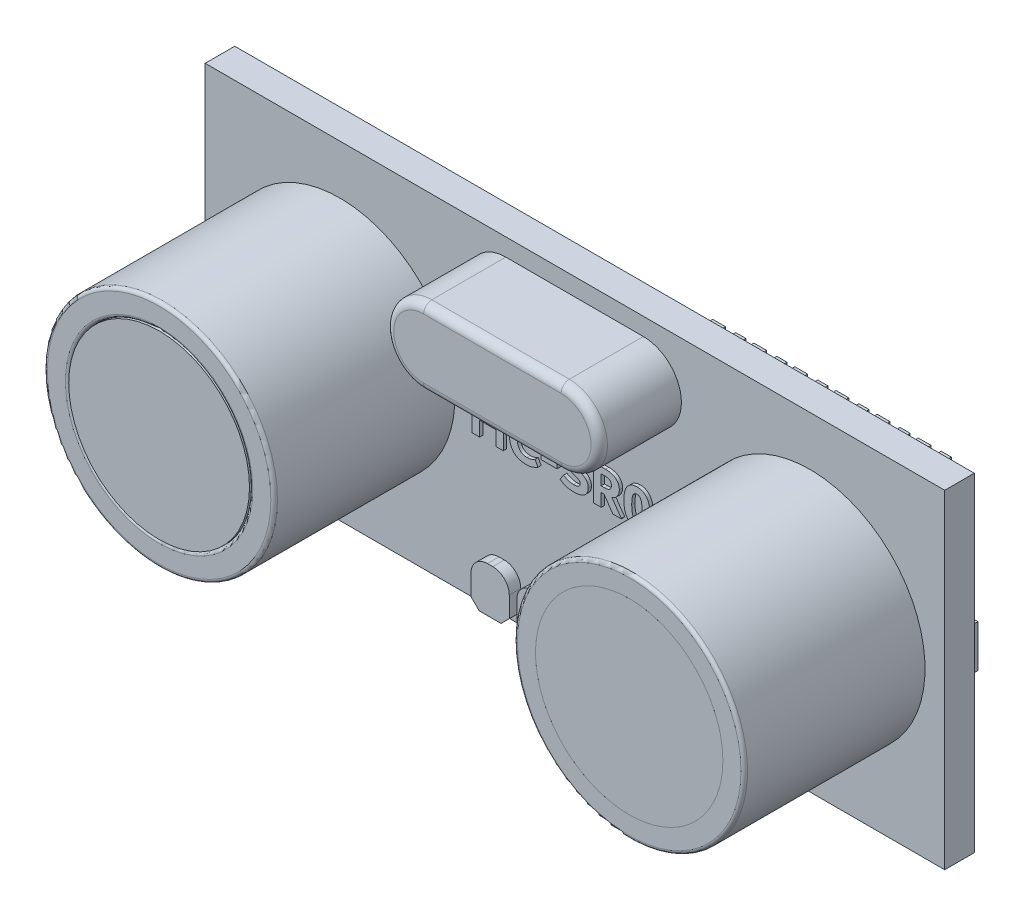
SolidWorks part; units mm, degrees
ref_plane "Front Plane" through (0, 0, 0) normal (0, 0, 1) x (1, 0, 0)
ref_plane "Top Plane" through (0, 0, 0) normal (0, 1, 0) x (1, 0, 0)
ref_plane "Right Plane" through (0, 0, 0) normal (1, 0, 0) x (0, 0, -1)
sketch "Sketch2" plane through (0, 0, 0) normal (0, 0, 1) x (1, 0, 0)
  line L1 (22.5, 10) -> (-22.5, 10)
  line L2 (22.5, 10) -> (22.5, -10)
  line L3 (22.5, -10) -> (-22.5, -10)
  line L4 (-22.5, 10) -> (-22.5, -10)
  line L5 (22.5, 10) -> (-22.5, -10) construction
  line L6 (22.5, -10) -> (-22.5, 10) construction
  point P0 (0, 0)
  dimension "D1" = 45
  dimension "D2" = 20
extrude "Boss-Extrude1" add sketch "Sketch2" along normal blind 1.8
sketch "Sketch3" plane through (0, 0, 1.8) normal (0, 0, 1) x (1, 0, 0)
  line L0 (0, 0) -> (0, -10) construction
  line L1 (-22.5, -10) -> (22.5, -10) construction
  line L2 (-22.5, 10) -> (-22.5, -10) construction
  line L3 (-22.5, 0) -> (22.5, 0) construction
  line L4 (22.5, -10) -> (22.5, 10) construction
  circle A0 centre (-14.3027, 0) radius 7
  circle A1 centre (-14.3027, 0) radius 5.5
  circle A2 centre (14.3027, 0) radius 5.5
  circle A3 centre (14.3027, 0) radius 7
extrude "Boss-Extrude2" add sketch "Sketch3" along normal blind 11
sketch "Sketch4" plane through (0, 0, 1.8) normal (0, 0, 1) x (1, 0, 0)
  line L0 (0, 0) -> (0, 5.0118) construction
  circle A0 centre (-14.3814, -0.1625) radius 3.6066
  circle A1 centre (14.3814, -0.1625) radius 3.6066
extrude "Boss-Extrude3" add sketch "Sketch4" along normal blind 3
sketch "Sketch5" plane through (0, 0, 1.8) normal (0, 0, 1) x (1, 0, 0)
  line L0 (0, 0) -> (0, 10) construction
  line L1 (22.5, 10) -> (-22.5, 10) construction
  line L2 (-4.2079, 6.6167) -> (4.1609, 6.6167) construction
  line L3 (-4.2079, 8.9335) -> (4.1609, 8.9335)
  line L4 (-4.2079, 4.2999) -> (4.1609, 4.2999)
  arc A0 (-4.2079, 8.9335) -> (-4.2079, 4.2999) centre (-4.2079, 6.6167) ccw
  arc A1 (4.1609, 4.2999) -> (4.1609, 8.9335) centre (4.1609, 6.6167) ccw
  point P7 (-0.0235, 6.6167)
extrude "Boss-Extrude4" add sketch "Sketch5" along normal blind 5
fillet "Fillet1" radius 0.5 4 edges at (-0.0235, 8.9335, 6.8) (6.4777, 6.6167, 6.8) (-0.0235, 4.2999, 6.8) (-6.5247, 6.6167, 6.8)
fillet "Fillet2" radius 0.2 4 edges at (8.8027, 0, 12.8) (7.3027, 0, 12.8) (-8.8027, 0, 12.8) (-7.3027, 0, 12.8)
sketch "Sketch6" plane through (0, 0, 12.8) normal (0, 0, 1) x (1, 0, 0)
  circle A0 centre (-14.3027, 0) radius 5.5
extrude "Boss-Extrude5" add sketch "Sketch6" against normal blind 0.2 separate body
sketch "Sketch7" plane through (0, 0, 12.8) normal (0, 0, 1) x (1, 0, 0)
  line L0 (0, 0) -> (0, -10.0616) construction
sketch "Sketch8" plane through (0, 0, 12.8) normal (0, 0, 1) x (1, 0, 0)
  circle A0 centre (14.3027, 0) radius 5.7
  circle A1 centre (14.3027, 0) radius 5.7
  circle M1 centre (14.3027, 0) radius 5.7
extrude "Boss-Extrude7" add sketch "Sketch8" against normal blind 0.3 separate body contours M1
sketch "Sketch9" plane through (0, 0, 1.8) normal (0, 0, 1) x (1, 0, 0)
  line L1 (-4.6238, -7.073) -> (-4.2964, -7.073)
  line L2 (-5.6238, -8.073) -> (-5.6238, -9.3177)
  line L3 (-5.1238, -9.8177) -> (-3.7964, -9.8177)
  line L4 (5.517, -8.073) -> (5.517, -9.3177)
  line L5 (2.9757, -9.3177) -> (3.4757, -9.8177)
  line L6 (5.517, -9.3177) -> (5.017, -9.8177)
  line L7 (-3.2964, -8.073) -> (-3.2964, -9.3177)
  line L8 (-2.8358, -8.073) -> (-2.8358, -9.3177)
  line L9 (-0.2685, -8.073) -> (-0.2685, -9.3177)
  line L10 (0.2992, -8.073) -> (0.2992, -9.3177)
  line L11 (3.9757, -7.073) -> (4.517, -7.073)
  line L12 (2.5161, -8.073) -> (2.5161, -9.3177)
  line L13 (2.9757, -8.073) -> (2.9757, -9.3177)
  line L14 (0.7992, -9.8177) -> (2.0161, -9.8177)
  line L15 (5.517, -11.7299) -> (5.7333, -11.7299)
  line L16 (1.2992, -7.073) -> (1.5161, -7.073)
  line L17 (-1.8358, -7.073) -> (-1.2685, -7.073)
  line L18 (-2.3358, -9.8177) -> (-0.7685, -9.8177)
  line L19 (3.4757, -9.8177) -> (5.017, -9.8177)
  line L20 (-5.6238, -9.3177) -> (-5.1238, -9.8177)
  line L21 (-3.7964, -9.8177) -> (-3.2964, -9.3177)
  line L22 (-2.8358, -9.3177) -> (-2.3358, -9.8177)
  line L23 (-0.2685, -9.3177) -> (-0.7685, -9.8177)
  line L24 (0.2992, -9.3177) -> (0.7992, -9.8177)
  line L25 (2.5161, -9.3177) -> (2.0161, -9.8177)
  line L26 (-0.2685, -8.48) -> (-0.2325, -8.4894) construction
  line L28 (-0.2685, -8.4983) -> (-0.2325, -8.4894) construction
  arc A0 (-4.6238, -7.073) -> (-5.6238, -8.073) centre (-4.6238, -8.073) ccw
  arc A1 (5.517, -8.073) -> (4.517, -7.073) centre (4.517, -8.073) ccw
  arc A2 (2.9757, -8.073) -> (3.9757, -7.073) centre (3.9757, -8.073) cw
  arc A3 (2.5161, -8.073) -> (1.5161, -7.073) centre (1.5161, -8.073) ccw
  arc A4 (0.2992, -8.073) -> (1.2992, -7.073) centre (1.2992, -8.073) cw
  arc A5 (-0.2685, -8.073) -> (-1.2685, -7.073) centre (-1.2685, -8.073) ccw
  arc A6 (-2.8358, -8.073) -> (-1.8358, -7.073) centre (-1.8358, -8.073) cw
  arc A7 (-3.2964, -8.073) -> (-4.2964, -7.073) centre (-4.2964, -8.073) ccw
  point P0 (-0.2325, -8.4894)
  point P8 (-3.2964, -9.8177)
  point P10 (-2.8358, -9.8177)
  point P12 (-0.2685, -9.8177)
  point P14 (0.2992, -9.8177)
  point P17 (2.5161, -9.8177)
  point P19 (2.9757, -9.8177)
  point P22 (5.517, -9.8177)
  point P30 (2.9757, -7.073)
  point P35 (0.2992, -7.073)
  point P40 (-2.8358, -7.073)
  dimension "D1" = 1
  dimension "D2" = 1
extrude "Boss-Extrude8" add sketch "Sketch9" along normal blind 0.7 contours L7 A7 L1 A0 L2 L20 L3 L21 | A6 L8 L22 L18 L23 L9 A5 L17 | A2 L13 L5 L19 L6 L4 A1 L11 | A4 L10 L24 L14 L25 L12 A3 L16
sketch "Sketch12" plane through (0, 0, 0) normal (0, 0, -1) x (-1, 0, 0)
  line L1 (-21.7259, 1.2905) -> (-14.7282, 1.2905)
  line L2 (-21.7259, 1.2905) -> (-21.7259, -1.2905)
  line L3 (-21.7259, -1.2905) -> (-14.7282, -1.2905)
  line L4 (-14.7282, 1.2905) -> (-14.7282, -1.2905)
  line L5 (-21.7259, 1.2905) -> (-14.7282, -1.2905) construction
  line L6 (-21.7259, -1.2905) -> (-14.7282, 1.2905) construction
  line L7 (-8.1561, 1.2905) -> (-0.8747, 1.2905)
  line L8 (-8.1561, 1.2905) -> (-8.1561, -1.2905)
  line L9 (-8.1561, -1.2905) -> (-0.8747, -1.2905)
  line L10 (-0.8747, 1.2905) -> (-0.8747, -1.2905)
  line L11 (-8.1561, 1.2905) -> (-0.8747, -1.2905) construction
  line L12 (-8.1561, -1.2905) -> (-0.8747, 1.2905) construction
  line L13 (12.7897, 4.0523) -> (16.3831, 4.0523)
  line L14 (12.7897, 4.0523) -> (12.7897, -3.1345)
  line L15 (12.7897, -3.1345) -> (16.3831, -3.1345)
  line L16 (16.3831, 4.0523) -> (16.3831, -3.1345)
  line L17 (12.7897, 4.0523) -> (16.3831, -3.1345) construction
  line L18 (12.7897, -3.1345) -> (16.3831, 4.0523) construction
  point P0 (-18.227, 0)
  point P5 (-4.5154, 0)
  point P10 (14.5864, 0.4589)
extrude "Boss-Extrude9" add sketch "Sketch12" along normal blind 1
sketch "Sketch13" plane through (0, 0, 0) normal (0, 0, -1) x (-1, 0, 0)
  line L0 (-17.8032, 9.3509) -> (-17.8032, 7.6448)
  line L1 (-20.3032, 9.3509) -> (-19.6828, 9.3509)
  line L2 (-20.3032, 9.3509) -> (-20.3032, 7.6448)
  line L3 (-20.3032, 7.6448) -> (-19.6828, 7.6448)
  line L4 (-19.6828, 9.3509) -> (-19.6828, 7.6448)
  line L5 (-20.3032, 9.3509) -> (-19.6828, 7.6448) construction
  line L6 (-20.3032, 7.6448) -> (-19.6828, 9.3509) construction
  line L7 (-19.0624, 9.3509) -> (-18.2869, 9.3509)
  line L8 (-19.0624, 9.3509) -> (-19.0624, 7.6448)
  line L9 (-19.0624, 7.6448) -> (-18.2869, 7.6448)
  line L10 (-18.2869, 9.3509) -> (-18.2869, 7.6448)
  line L11 (-19.0624, 9.3509) -> (-18.2869, 7.6448) construction
  line L12 (-19.0624, 7.6448) -> (-18.2869, 9.3509) construction
  line L13 (-17.8032, 9.3509) -> (-17.1828, 9.3509)
  line L14 (-17.1828, 9.3509) -> (-17.1828, 7.6448)
  line L15 (-17.8032, 7.6448) -> (-17.1828, 7.6448)
  line L16 (-17.8032, 7.6448) -> (-17.1828, 9.3509) construction
  line L17 (-17.8032, 9.3509) -> (-17.1828, 7.6448) construction
  line L18 (-16.5624, 9.3509) -> (-16.5624, 7.6448)
  line L19 (-16.5624, 7.6448) -> (-15.7869, 7.6448)
  line L20 (-16.5624, 7.6448) -> (-15.7869, 9.3509) construction
  line L21 (-16.5624, 9.3509) -> (-15.7869, 7.6448) construction
  line L22 (-16.5624, 9.3509) -> (-15.7869, 9.3509)
  line L23 (-15.7869, 9.3509) -> (-15.7869, 7.6448)
  line L24 (-15.3032, 9.3509) -> (-15.3032, 7.6448)
  line L25 (-15.3032, 9.3509) -> (-14.6828, 9.3509)
  line L26 (-14.6828, 9.3509) -> (-14.6828, 7.6448)
  line L27 (-15.3032, 7.6448) -> (-14.6828, 7.6448)
  line L28 (-15.3032, 7.6448) -> (-14.6828, 9.3509) construction
  line L29 (-15.3032, 9.3509) -> (-14.6828, 7.6448) construction
  line L30 (-14.0624, 9.3509) -> (-14.0624, 7.6448)
  line L31 (-14.0624, 7.6448) -> (-13.2869, 7.6448)
  line L32 (-14.0624, 7.6448) -> (-13.2869, 9.3509) construction
  line L33 (-14.0624, 9.3509) -> (-13.2869, 7.6448) construction
  line L34 (-14.0624, 9.3509) -> (-13.2869, 9.3509)
  line L35 (-13.2869, 9.3509) -> (-13.2869, 7.6448)
  line L36 (-12.8032, 9.3509) -> (-12.8032, 7.6448)
  line L37 (-12.8032, 9.3509) -> (-12.1828, 9.3509)
  line L38 (-12.1828, 9.3509) -> (-12.1828, 7.6448)
  line L39 (-12.8032, 7.6448) -> (-12.1828, 7.6448)
  line L40 (-12.8032, 7.6448) -> (-12.1828, 9.3509) construction
  line L41 (-12.8032, 9.3509) -> (-12.1828, 7.6448) construction
  line L42 (-11.5624, 9.3509) -> (-11.5624, 7.6448)
  line L43 (-11.5624, 7.6448) -> (-10.7869, 7.6448)
  line L44 (-11.5624, 7.6448) -> (-10.7869, 9.3509) construction
  line L45 (-11.5624, 9.3509) -> (-10.7869, 7.6448) construction
  line L46 (-11.5624, 9.3509) -> (-10.7869, 9.3509)
  line L47 (-10.7869, 9.3509) -> (-10.7869, 7.6448)
  line L48 (-10.3032, 9.3509) -> (-10.3032, 7.6448)
  line L49 (-10.3032, 9.3509) -> (-9.6828, 9.3509)
  line L50 (-9.6828, 9.3509) -> (-9.6828, 7.6448)
  line L51 (-10.3032, 7.6448) -> (-9.6828, 7.6448)
  line L52 (-10.3032, 7.6448) -> (-9.6828, 9.3509) construction
  line L53 (-10.3032, 9.3509) -> (-9.6828, 7.6448) construction
  line L54 (-9.0624, 9.3509) -> (-9.0624, 7.6448)
  line L55 (-9.0624, 7.6448) -> (-8.2869, 7.6448)
  line L56 (-9.0624, 7.6448) -> (-8.2869, 9.3509) construction
  line L57 (-9.0624, 9.3509) -> (-8.2869, 7.6448) construction
  line L58 (-9.0624, 9.3509) -> (-8.2869, 9.3509)
  line L59 (-8.2869, 9.3509) -> (-8.2869, 7.6448)
  line L60 (-7.8032, 9.3509) -> (-7.8032, 7.6448)
  line L61 (-7.8032, 9.3509) -> (-7.1828, 9.3509)
  line L62 (-7.1828, 9.3509) -> (-7.1828, 7.6448)
  line L63 (-7.8032, 7.6448) -> (-7.1828, 7.6448)
  line L64 (-7.8032, 7.6448) -> (-7.1828, 9.3509) construction
  line L65 (-7.8032, 9.3509) -> (-7.1828, 7.6448) construction
  line L66 (-6.5624, 9.3509) -> (-6.5624, 7.6448)
  line L67 (-6.5624, 7.6448) -> (-5.7869, 7.6448)
  line L68 (-6.5624, 7.6448) -> (-5.7869, 9.3509) construction
  line L69 (-6.5624, 9.3509) -> (-5.7869, 7.6448) construction
  line L70 (-6.5624, 9.3509) -> (-5.7869, 9.3509)
  line L71 (-5.7869, 9.3509) -> (-5.7869, 7.6448)
  line L72 (-17.8032, -4.6491) -> (-17.8032, -6.3552)
  line L73 (-17.8032, -4.6491) -> (-17.1828, -4.6491)
  line L74 (-17.1828, -4.6491) -> (-17.1828, -6.3552)
  line L75 (-17.8032, -6.3552) -> (-17.1828, -6.3552)
  line L76 (-17.8032, -6.3552) -> (-17.1828, -4.6491) construction
  line L77 (-17.8032, -4.6491) -> (-17.1828, -6.3552) construction
  line L78 (-16.5624, -4.6491) -> (-16.5624, -6.3552)
  line L79 (-16.5624, -6.3552) -> (-15.7869, -6.3552)
  line L80 (-16.5624, -6.3552) -> (-15.7869, -4.6491) construction
  line L81 (-16.5624, -4.6491) -> (-15.7869, -6.3552) construction
  line L82 (-16.5624, -4.6491) -> (-15.7869, -4.6491)
  line L83 (-15.7869, -4.6491) -> (-15.7869, -6.3552)
  line L84 (-15.3032, -4.6491) -> (-15.3032, -6.3552)
  line L85 (-15.3032, -4.6491) -> (-14.6828, -4.6491)
  line L86 (-14.6828, -4.6491) -> (-14.6828, -6.3552)
  line L87 (-15.3032, -6.3552) -> (-14.6828, -6.3552)
  line L88 (-15.3032, -6.3552) -> (-14.6828, -4.6491) construction
  line L89 (-15.3032, -4.6491) -> (-14.6828, -6.3552) construction
  line L90 (-14.0624, -4.6491) -> (-14.0624, -6.3552)
  line L91 (-14.0624, -6.3552) -> (-13.2869, -6.3552)
  line L92 (-14.0624, -6.3552) -> (-13.2869, -4.6491) construction
  line L93 (-14.0624, -4.6491) -> (-13.2869, -6.3552) construction
  line L94 (-14.0624, -4.6491) -> (-13.2869, -4.6491)
  line L95 (-13.2869, -4.6491) -> (-13.2869, -6.3552)
  line L96 (-12.8032, -4.6491) -> (-12.8032, -6.3552)
  line L97 (-12.8032, -4.6491) -> (-12.1828, -4.6491)
  line L98 (-12.1828, -4.6491) -> (-12.1828, -6.3552)
  line L99 (-12.8032, -6.3552) -> (-12.1828, -6.3552)
  line L100 (-12.8032, -6.3552) -> (-12.1828, -4.6491) construction
  line L101 (-12.8032, -4.6491) -> (-12.1828, -6.3552) construction
  line L102 (-11.5624, -4.6491) -> (-11.5624, -6.3552)
  line L103 (-11.5624, -6.3552) -> (-10.7869, -6.3552)
  line L104 (-11.5624, -6.3552) -> (-10.7869, -4.6491) construction
  line L105 (-11.5624, -4.6491) -> (-10.7869, -6.3552) construction
  line L106 (-11.5624, -4.6491) -> (-10.7869, -4.6491)
  line L107 (-10.7869, -4.6491) -> (-10.7869, -6.3552)
  line L108 (-10.3032, -4.6491) -> (-10.3032, -6.3552)
  line L109 (-10.3032, -4.6491) -> (-9.6828, -4.6491)
  line L110 (-9.6828, -4.6491) -> (-9.6828, -6.3552)
  line L111 (-10.3032, -6.3552) -> (-9.6828, -6.3552)
  line L112 (-10.3032, -6.3552) -> (-9.6828, -4.6491) construction
  line L113 (-10.3032, -4.6491) -> (-9.6828, -6.3552) construction
  line L114 (-9.0624, -4.6491) -> (-9.0624, -6.3552)
  line L115 (-9.0624, -6.3552) -> (-8.2869, -6.3552)
  line L116 (-9.0624, -6.3552) -> (-8.2869, -4.6491) construction
  line L117 (-9.0624, -4.6491) -> (-8.2869, -6.3552) construction
  line L118 (-9.0624, -4.6491) -> (-8.2869, -4.6491)
  line L119 (-8.2869, -4.6491) -> (-8.2869, -6.3552)
  line L120 (-7.8032, -4.6491) -> (-7.8032, -6.3552)
  line L121 (-7.8032, -4.6491) -> (-7.1828, -4.6491)
  line L122 (-7.1828, -4.6491) -> (-7.1828, -6.3552)
  line L123 (-7.8032, -6.3552) -> (-7.1828, -6.3552)
  line L124 (-7.8032, -6.3552) -> (-7.1828, -4.6491) construction
  line L125 (-7.8032, -4.6491) -> (-7.1828, -6.3552) construction
  line L126 (-6.5624, -4.6491) -> (-6.5624, -6.3552)
  line L127 (-6.5624, -6.3552) -> (-5.7869, -6.3552)
  line L128 (-6.5624, -6.3552) -> (-5.7869, -4.6491) construction
  line L129 (-6.5624, -4.6491) -> (-5.7869, -6.3552) construction
  line L130 (-6.5624, -4.6491) -> (-5.7869, -4.6491)
  line L131 (-5.7869, -4.6491) -> (-5.7869, -6.3552)
  line L132 (-20.3032, -4.6491) -> (-20.3032, -6.3552)
  line L133 (-20.3032, -4.6491) -> (-19.6828, -4.6491)
  line L134 (-19.6828, -4.6491) -> (-19.6828, -6.3552)
  line L135 (-20.3032, -6.3552) -> (-19.6828, -6.3552)
  line L136 (-20.3032, -6.3552) -> (-19.6828, -4.6491) construction
  line L137 (-20.3032, -4.6491) -> (-19.6828, -6.3552) construction
  line L138 (-19.0624, -4.6491) -> (-19.0624, -6.3552)
  line L139 (-19.0624, -6.3552) -> (-18.2869, -6.3552)
  line L140 (-19.0624, -6.3552) -> (-18.2869, -4.6491) construction
  line L141 (-19.0624, -4.6491) -> (-18.2869, -6.3552) construction
  line L142 (-19.0624, -4.6491) -> (-18.2869, -4.6491)
  line L143 (-18.2869, -4.6491) -> (-18.2869, -6.3552)
  point P0 (-19.993, 8.4978)
  point P5 (-18.6746, 8.4978)
  dimension "D1" = 6
  dimension "D2" = 2
extrude "Boss-Extrude10" add sketch "Sketch13" along normal blind 0.8
sketch "Sketch15" plane through (0, 0, 0) normal (0, 0, -1) x (-1, 0, 0)
  line L0 (4.8255, 2.9186) -> (4.0469, 2.9186)
  line L1 (4.8255, 0.7912) -> (4.8255, -1.0904)
  line L2 (4.8255, 0.7912) -> (4.0469, 0.7912)
  line L3 (4.0469, 0.7912) -> (4.0469, -1.0904)
  line L4 (4.8255, -1.0904) -> (4.0469, -1.0904)
  line L5 (4.8255, 0.7912) -> (4.0469, -1.0904) construction
  line L6 (4.0469, 0.7912) -> (4.8255, -1.0904) construction
  line L7 (4.8255, 4.8002) -> (4.0469, 2.9186) construction
  line L8 (4.0469, 4.8002) -> (4.0469, 2.9186)
  line L9 (4.8255, 4.8002) -> (4.0469, 4.8002)
  line L10 (4.0469, 4.8002) -> (4.8255, 2.9186) construction
  line L11 (4.8255, 4.8002) -> (4.8255, 2.9186)
  line L12 (3.2077, 0.7103) -> (2.4291, 0.7103)
  line L13 (3.2077, 2.592) -> (3.2077, 0.7103)
  line L14 (3.2077, 2.592) -> (2.4291, 0.7103) construction
  line L15 (3.2077, 2.592) -> (2.4291, 2.592)
  line L16 (2.4291, 2.592) -> (2.4291, 0.7103)
  line L17 (2.4291, 2.592) -> (3.2077, 0.7103) construction
  line L18 (14.3374, -7.7932) -> (16.2191, -7.7932)
  line L19 (14.0108, -5.3969) -> (14.0108, -6.1755)
  line L20 (12.1292, -5.3969) -> (12.1292, -6.1755)
  line L21 (18.0198, -5.3969) -> (18.0198, -6.1755)
  line L22 (12.1292, -6.1755) -> (14.0108, -6.1755)
  line L23 (16.1382, -5.3969) -> (16.1382, -6.1755)
  line L24 (14.3374, -7.0146) -> (16.2191, -7.0146)
  line L25 (12.1292, -5.3969) -> (14.0108, -5.3969)
  line L26 (12.1292, -6.1755) -> (14.0108, -5.3969) construction
  line L27 (14.3374, -7.0146) -> (16.2191, -7.7932) construction
  line L28 (12.1292, -5.3969) -> (14.0108, -6.1755) construction
  line L29 (14.3374, -7.0146) -> (14.3374, -7.7932)
  line L30 (16.2191, -7.0146) -> (16.2191, -7.7932)
  line L31 (16.1382, -6.1755) -> (18.0198, -5.3969) construction
  line L32 (16.1382, -6.1755) -> (18.0198, -6.1755)
  line L33 (16.1382, -5.3969) -> (18.0198, -6.1755) construction
  line L34 (16.1382, -5.3969) -> (18.0198, -5.3969)
  line L35 (14.3374, -7.7932) -> (16.2191, -7.0146) construction
  line L36 (-12.3479, 3.2689) -> (-12.3479, 2.4903)
  line L37 (-10.4663, 3.2689) -> (-10.4663, 2.4903)
  line L38 (-12.3479, 3.2689) -> (-10.4663, 2.4903) construction
  line L39 (-12.3479, 2.4903) -> (-10.4663, 2.4903)
  line L40 (-12.3479, 2.4903) -> (-10.4663, 3.2689) construction
  line L41 (-12.3479, 3.2689) -> (-10.4663, 3.2689)
  line L42 (0.5142, 8.9122) -> (0.5142, 8.1336)
  line L43 (12.9207, 8.9122) -> (12.9207, 8.1336)
  line L44 (0.5142, 8.1336) -> (2.3958, 8.9122) construction
  line L45 (18.8113, 8.9122) -> (18.8113, 8.1336)
  line L46 (16.9297, 8.1336) -> (18.8113, 8.9122) construction
  line L47 (16.9297, 8.9122) -> (16.9297, 8.1336)
  line L48 (2.3958, 8.9122) -> (2.3958, 8.1336)
  line L49 (12.9207, 8.1336) -> (14.8024, 8.1336)
  line L50 (12.9207, 8.9122) -> (14.8024, 8.1336) construction
  line L51 (0.5142, 8.1336) -> (2.3958, 8.1336)
  line L52 (0.5142, 8.9122) -> (2.3958, 8.9122)
  line L53 (14.8024, 8.9122) -> (14.8024, 8.1336)
  line L54 (12.9207, 8.9122) -> (14.8024, 8.9122)
  line L55 (16.9297, 8.1336) -> (18.8113, 8.1336)
  line L56 (12.9207, 8.1336) -> (14.8024, 8.9122) construction
  line L57 (16.9297, 8.9122) -> (18.8113, 8.1336) construction
  line L58 (16.9297, 8.9122) -> (18.8113, 8.9122)
  line L59 (0.5142, 8.9122) -> (2.3958, 8.1336) construction
  line L60 (8.1525, 4.8002) -> (7.3739, 2.9186) construction
  line L61 (8.1525, 2.9186) -> (7.3739, 2.9186)
  line L62 (5.7561, 2.592) -> (5.7561, 0.7103)
  line L63 (8.1525, 0.7912) -> (8.1525, -1.0904)
  line L64 (6.5348, 2.592) -> (5.7561, 0.7103) construction
  line L65 (6.5348, 0.7103) -> (5.7561, 0.7103)
  line L66 (5.7561, 2.592) -> (6.5348, 0.7103) construction
  line L67 (8.1525, -1.0904) -> (7.3739, -1.0904)
  line L68 (7.3739, 4.8002) -> (7.3739, 2.9186)
  line L69 (8.1525, 0.7912) -> (7.3739, -1.0904) construction
  line L70 (7.3739, 0.7912) -> (7.3739, -1.0904)
  line L71 (6.5348, 2.592) -> (6.5348, 0.7103)
  line L72 (8.1525, 4.8002) -> (7.3739, 4.8002)
  line L73 (7.3739, 0.7912) -> (8.1525, -1.0904) construction
  line L74 (8.1525, 0.7912) -> (7.3739, 0.7912)
  line L75 (6.5348, 2.592) -> (5.7561, 2.592)
  line L76 (7.3739, 4.8002) -> (8.1525, 2.9186) construction
  line L77 (8.1525, 4.8002) -> (8.1525, 2.9186)
  line L78 (-14.8758, 2.3281) -> (-15.6544, 2.3281)
  line L79 (-15.6544, 4.2097) -> (-14.8758, 2.3281) construction
  line L80 (-14.8758, 4.2097) -> (-15.6544, 4.2097)
  line L81 (-14.8758, 4.2097) -> (-15.6544, 2.3281) construction
  line L82 (-14.8758, 4.2097) -> (-14.8758, 2.3281)
  line L83 (-15.6544, 4.2097) -> (-15.6544, 2.3281)
  line L84 (11.0952, -2.2608) -> (11.0952, -3.0394)
  line L85 (5.2046, -2.2608) -> (5.2046, -3.0394)
  line L86 (9.2136, -2.2608) -> (11.0952, -2.2608)
  line L87 (9.2136, -2.2608) -> (9.2136, -3.0394)
  line L88 (5.2046, -3.0394) -> (7.0863, -3.0394)
  line L89 (9.2136, -3.0394) -> (11.0952, -3.0394)
  line L90 (5.2046, -2.2608) -> (7.0863, -3.0394) construction
  line L91 (7.0863, -2.2608) -> (7.0863, -3.0394)
  line L92 (9.2136, -3.0394) -> (11.0952, -2.2608) construction
  line L93 (9.2136, -2.2608) -> (11.0952, -3.0394) construction
  line L94 (5.2046, -3.0394) -> (7.0863, -2.2608) construction
  line L95 (5.2046, -2.2608) -> (7.0863, -2.2608)
  point P0 (4.4362, -0.1496)
  point P5 (4.4362, 3.8594)
  point P10 (2.8184, 1.6511)
  point P15 (17.079, -5.7862)
  point P20 (13.07, -5.7862)
  point P25 (15.2783, -7.4039)
  point P30 (17.8705, 8.5229)
  point P32 (-11.4071, 2.8796)
  point P40 (13.8616, 8.5229)
  point P45 (1.455, 8.5229)
  point P50 (7.7632, -0.1496)
  point P55 (7.7632, 3.8594)
  point P60 (6.1454, 1.6511)
  point P65 (-15.2651, 3.2689)
  point P70 (10.1544, -2.6501)
  point P75 (6.1454, -2.6501)
extrude "Boss-Extrude11" add sketch "Sketch15" along normal blind 0.8
sketch "Sketch16" plane through (0, 0, 1.8) normal (0, 0, 1) x (1, 0, 0)
  text T0 "HC-SR04" font "Dubai" height in points 8
extrude "Boss-Extrude12" add sketch "Sketch16" along normal blind 0.2
